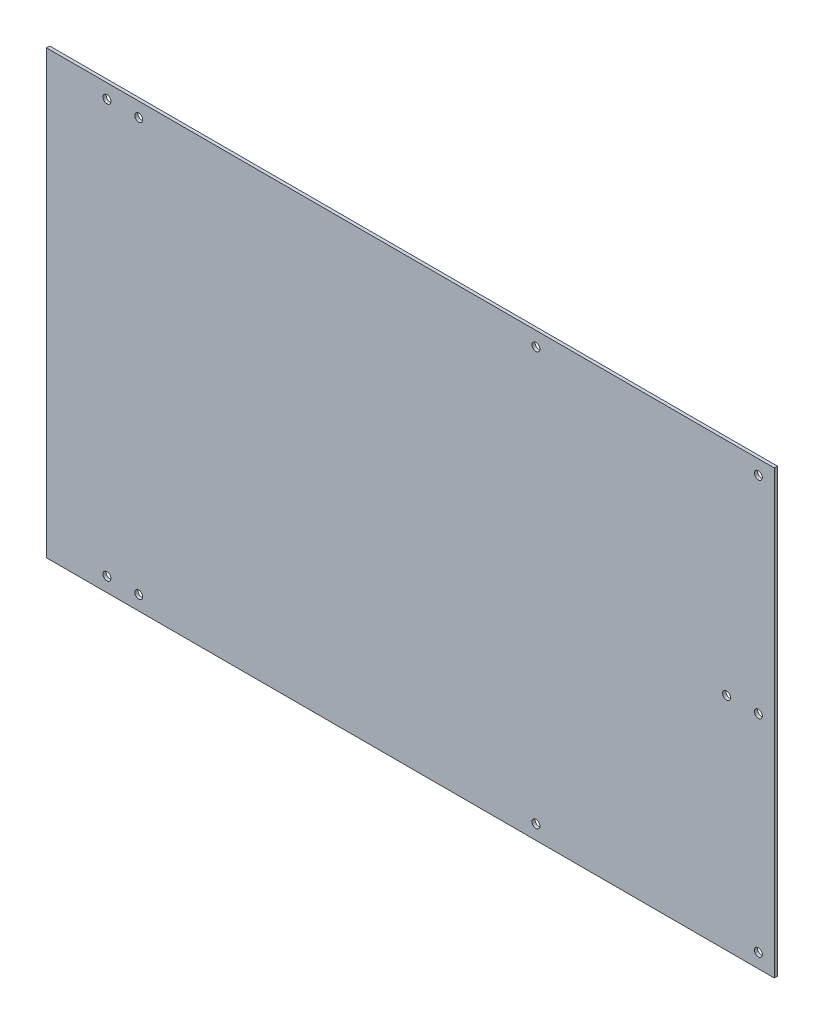
SolidWorks part; units mm, degrees
ref_plane "前视基准面" through (0, 0, 0) normal (0, 0, 1) x (1, 0, 0)
ref_plane "上视基准面" through (0, 0, 0) normal (0, 1, 0) x (1, 0, 0)
ref_plane "右视基准面" through (0, 0, 0) normal (1, 0, 0) x (0, 0, -1)
sketch "草图1" plane through (0, 0, 0) normal (0, 0, 1) x (1, 0, 0)
  line L0 (-113.5092, 42.3638) -> (344.4908, 42.3638)
  line L2 (344.4908, -235.6362) -> (-113.5092, -235.6362)
  line L3 (-113.5092, -235.6362) -> (-113.5092, 42.3638)
  line L4 (344.4908, 42.3638) -> (344.4908, -235.6362)
  line L5 (344.4908, -96.6362) -> (-113.5092, -96.6362) construction
  line L6 (115.4908, 42.3638) -> (115.4908, -235.6362) construction
  line L7 (334.4908, -226.6362) -> (194.4908, -226.6362) construction
  line L8 (344.4908, -96.6362) -> (334.4908, -96.6362) construction
  line L9 (334.4908, -96.6362) -> (314.4908, -96.6362) construction
  circle A0 centre (334.4908, -226.6362) radius 2.5
  circle A1 centre (194.4908, -226.6362) radius 2.5
  circle A2 centre (194.4908, 33.3638) radius 2.5
  circle A3 centre (334.4908, 33.3638) radius 2.5
  circle A8 centre (-55.5092, 33.3638) radius 2.5
  circle A9 centre (-75.5092, 33.3638) radius 2.5
  circle A10 centre (-75.5092, -226.6362) radius 2.5
  circle A11 centre (-55.5092, -226.6362) radius 2.5
  circle A12 centre (334.4908, -96.6362) radius 2.5
  circle A13 centre (314.4908, -96.6362) radius 2.5
  dimension "D6" = 5
  dimension "D7" = 20
  dimension "D4" = 5
  dimension "D9" = 5
  dimension "D10" = 5
  dimension "D11" = 5
  dimension "D12" = 5
  dimension "D1" = 458
  dimension "D2" = 278
  dimension "D3" = 140
  dimension "D5" = 10
  dimension "D8" = 20
extrude "凸台-拉伸1" add sketch "草图1" along normal blind 2
